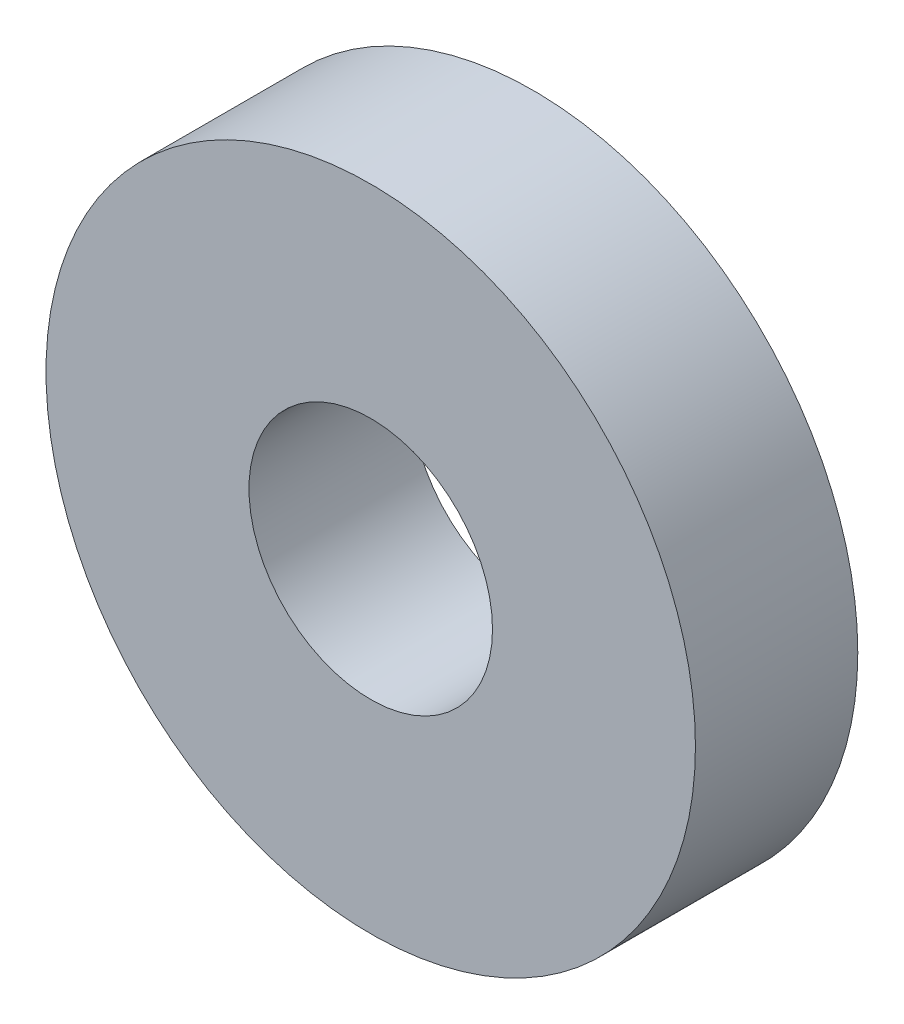
SolidWorks part; units mm, degrees
ref_plane "Plano frontal" through (0, 0, 0) normal (0, 0, 1) x (1, 0, 0)
ref_plane "Plano superior" through (0, 0, 0) normal (0, 1, 0) x (1, 0, 0)
ref_plane "Plano direito" through (0, 0, 0) normal (1, 0, 0) x (0, 0, -1)
sketch "Esboço1" plane through (0, 0, 0) normal (0, 0, 1) x (1, 0, 0)
  circle A0 centre (0, 0) radius 3
  circle A1 centre (0, 0) radius 8
extrude "Ressalto-extrusão1" add sketch "Esboço1" along normal blind 4
